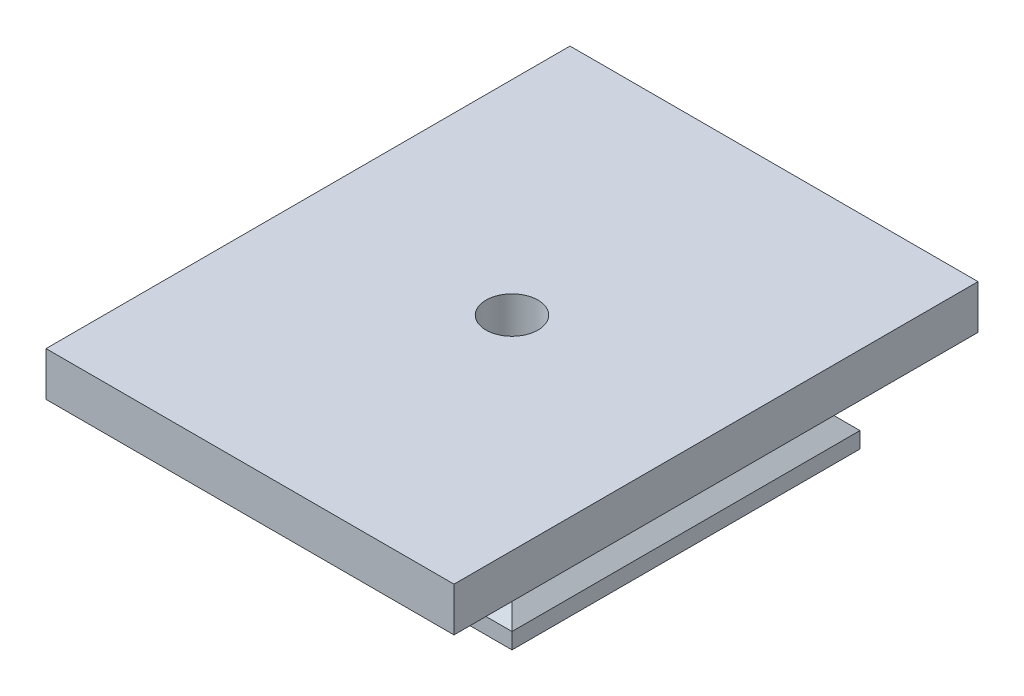
SolidWorks part; units mm, degrees
ref_plane "Front Plane" through (0, 0, 0) normal (0, 0, 1) x (1, 0, 0)
ref_plane "Top Plane" through (0, 0, 0) normal (0, 1, 0) x (1, 0, 0)
ref_plane "Right Plane" through (0, 0, 0) normal (1, 0, 0) x (0, 0, -1)
sketch "Sketch1" plane through (0, 0, 0) normal (0, 1, 0) x (1, 0, 0)
  line L1 (-27.7005, 18.3644) -> (15.7995, 18.3644)
  line L2 (-27.7005, 18.3644) -> (-27.7005, -25.1356)
  line L3 (-27.7005, -25.1356) -> (15.7995, -25.1356)
  line L4 (15.7995, 18.3644) -> (15.7995, -25.1356)
  dimension "D1" = 43.5
  dimension "D2" = 43.5
extrude "Boss-Extrude1" add sketch "Sketch1" along normal blind 2
sketch "Sketch2" plane through (0, 2, 0) normal (0, 1, 0) x (1, 0, 0)
  line L1 (-27.7005, 18.3644) -> (15.7995, 18.3644)
  line L2 (-27.7005, 18.3644) -> (-27.7005, -25.1356)
  line L3 (-27.7005, -25.1356) -> (15.7995, -25.1356)
  line L4 (15.7995, 18.3644) -> (15.7995, -25.1356)
extrude "Boss-Extrude3" add sketch "Sketch2" along normal blind 7 separate body
sketch "Sketch4" plane through (0, 9, 0) normal (0, 1, 0) x (1, 0, 0)
  line L0 (-20.7005, 11.3644) -> (-20.7005, -18.1356)
  line L1 (-27.7005, 18.3644) -> (15.7995, 18.3644)
  line L2 (-27.7005, 18.3644) -> (-27.7005, -25.1356)
  line L3 (-27.7005, -25.1356) -> (15.7995, -25.1356)
  line L4 (15.7995, 18.3644) -> (15.7995, -25.1356)
  line L5 (-20.7005, -18.1356) -> (8.7995, -18.1356)
  line L6 (8.7995, 11.3644) -> (8.7995, -18.1356)
  line L7 (-20.7005, 11.3644) -> (8.7995, 11.3644)
  dimension "D1" = 7
sketch "Sketch5" plane through (0, 0, 25.1356) normal (0, 0, 1) x (1, 0, 0)
  line L0 (-27.7005, 2) -> (-20.7005, 9)
  line L1 (-27.7005, 9) -> (-20.7005, 9)
  line L2 (-27.7005, 9) -> (-27.7005, 2)
  line L3 (15.7995, 9) -> (15.7995, 2)
  line L4 (15.7995, 2) -> (8.7995, 9)
  line L5 (-20.7005, 9) -> (-27.7005, 9)
  line L6 (-27.7005, 9) -> (15.7995, 9) construction
  line L7 (8.7995, 9) -> (15.7995, 9)
  line M4 (15.7995, 2) -> (15.7995, 9)
  line M5 (15.7995, 9) -> (-27.7005, 9)
  line M6 (-27.7005, 9) -> (-27.7005, 2)
  dimension "D1" = 7
  dimension "D2" = 7
extrude "Cut-Extrude1" cut sketch "Sketch5" against normal through all contours L4 M4 M5 | L0 M6 M5
sketch "Sketch6" plane through (15.7995, 0, 0) normal (1, 0, 0) x (0, 0, -1)
  line L0 (-25.1356, 2) -> (-25.1356, 9)
  line L1 (-25.1356, 9) -> (-18.1356, 9)
  line L2 (18.3644, 9) -> (-25.1356, 9) construction
  line L3 (-18.1356, 9) -> (-25.1356, 2)
  line L4 (18.3644, 2) -> (18.3644, 9)
  line L5 (18.3644, 9) -> (11.3644, 9)
  line L6 (11.3644, 9) -> (18.3644, 2)
  dimension "D1" = 7
  dimension "D2" = 7
extrude "Cut-Extrude2" cut sketch "Sketch6" against normal through all
sketch "Sketch7" plane through (0, 9, 0) normal (0, 1, 0) x (1, 0, 0)
  line L2 (19.5495, -36.1356) -> (-31.4505, -36.1356)
  line L3 (19.5495, -36.1356) -> (19.5495, 29.3644)
  line L4 (19.5495, 29.3644) -> (-31.4505, 29.3644)
  line L5 (-31.4505, -36.1356) -> (-31.4505, 29.3644)
  line L6 (19.5495, -36.1356) -> (-31.4505, 29.3644) construction
  line L7 (19.5495, 29.3644) -> (-31.4505, -36.1356) construction
  point P4 (-5.9505, -3.3856)
  dimension "D1" = 51
  dimension "D2" = 65.5
extrude "Boss-Extrude4" add sketch "Sketch7" along normal blind 5.5
sketch "Sketch8" plane through (0, 0, 0) normal (0, -1, 0) x (1, 0, 0)
  line L0 (-27.7005, 25.1356) -> (15.7995, -18.3644) construction
  line L1 (15.7995, -18.3644) -> (-27.7005, -18.3644) construction
  circle A0 centre (-5.9505, 3.3856) radius 3.25
  dimension "D1" = 6.5
extrude "Cut-Extrude3" cut sketch "Sketch8" against normal through all
sketch "Sketch9" plane through (0, 0, 0) normal (0, -1, 0) x (1, 0, 0)
  line L1 (-5.9505, -3.2539) -> (-0.2005, 0.0658)
  line L2 (-0.2005, 0.0658) -> (-0.2005, 6.7054)
  line L3 (-0.2005, 6.7054) -> (-5.9505, 10.0251)
  line L4 (-5.9505, 10.0251) -> (-11.7005, 6.7054)
  line L5 (-11.7005, 6.7054) -> (-11.7005, 0.0658)
  line L6 (-11.7005, 0.0658) -> (-5.9505, -3.2539)
  circle A0 centre (-5.9505, 3.3856) radius 5.75 construction
  dimension "D1" = 11.5
extrude "Cut-Extrude4" cut sketch "Sketch9" against normal blind 6
